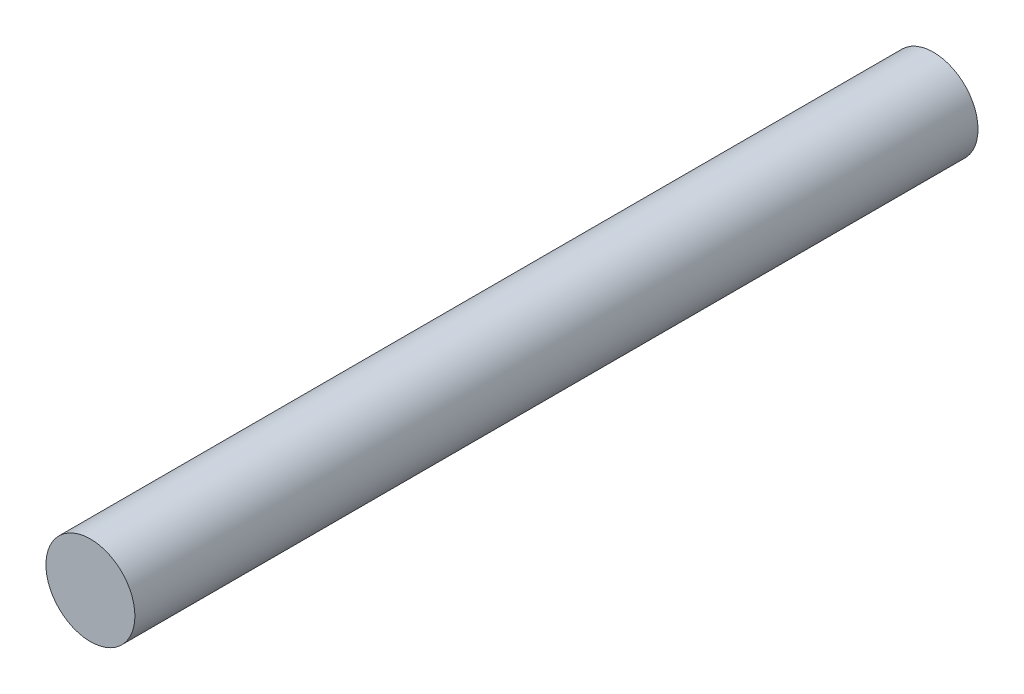
SolidWorks part; units mm, degrees
ref_plane "Front Plane" through (0, 0, 0) normal (0, 0, 1) x (1, 0, 0)
ref_plane "Top Plane" through (0, 0, 0) normal (0, 1, 0) x (1, 0, 0)
ref_plane "Right Plane" through (0, 0, 0) normal (1, 0, 0) x (0, 0, -1)
sketch "Sketch1" plane through (0, 0, 0) normal (0, 0, 1) x (1, 0, 0)
  circle A0 centre (0, 0) radius 4.75
  dimension "D1" = 9.5
extrude "Boss-Extrude1" add sketch "Sketch1" along normal blind 90
